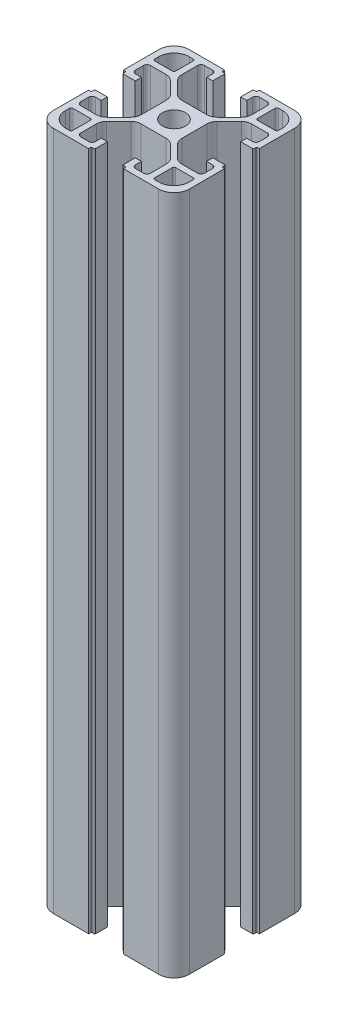
SolidWorks part; units mm, degrees
ref_plane "Front Plane" through (0, 0, 0) normal (0, 0, 1) x (1, 0, 0)
ref_plane "Top Plane" through (0, 0, 0) normal (0, 1, 0) x (1, 0, 0)
ref_plane "Right Plane" through (0, 0, 0) normal (1, 0, 0) x (0, 0, -1)
sketch "Sketch1" plane through (0, 0, 0) normal (0, 1, 0) x (1, 0, 0)
  line L0 (84.1702, 31.7204) -> (84.1702, 42.1204)
  line L1 (44.1702, 62.7204) -> (44.1702, 52.3204)
  line L2 (48.6702, 27.2204) -> (59.0702, 27.2204)
  line L3 (79.6702, 67.2204) -> (69.4702, 67.2204)
  line L4 (84.1702, 52.3204) -> (84.1702, 62.7204)
  line L5 (58.8702, 67.2204) -> (48.6702, 67.2204)
  line L6 (44.1702, 42.1204) -> (44.1702, 31.7204)
  line L7 (69.2702, 27.2204) -> (79.6702, 27.2204)
  line L10 (44.1702, 42.1204) -> (44.7702, 42.1204)
  line L11 (44.9702, 42.3204) -> (44.9702, 42.9204)
  line L12 (48.6702, 43.1204) -> (45.1702, 43.1204)
  line L13 (48.6702, 41.3204) -> (48.6702, 43.1204)
  line L14 (46.9702, 41.3204) -> (48.6702, 41.3204)
  line L15 (45.9702, 37.9704) -> (45.9702, 40.3204)
  line L16 (51.6169, 36.9704) -> (46.9702, 36.9704)
  line L17 (57.2915, 41.4024) -> (53.7382, 37.8491)
  line L18 (58.1702, 50.9171) -> (58.1702, 43.5237)
  line L19 (53.7382, 56.5917) -> (57.2915, 53.0384)
  line L20 (46.9702, 57.4704) -> (51.6169, 57.4704)
  line L21 (45.9702, 54.1204) -> (45.9702, 56.4704)
  line L22 (48.6702, 53.1204) -> (46.9702, 53.1204)
  line L23 (48.6702, 51.3204) -> (48.6702, 53.1204)
  line L24 (45.1702, 51.3204) -> (48.6702, 51.3204)
  line L25 (44.9702, 51.5204) -> (44.9702, 52.1204)
  line L26 (44.7702, 52.3204) -> (44.1702, 52.3204)
  line L29 (59.0702, 67.0204) -> (59.0702, 66.6204)
  line L30 (59.2702, 66.4204) -> (59.8702, 66.4204)
  line L31 (60.0702, 62.7204) -> (60.0702, 66.2204)
  line L32 (58.2702, 62.7204) -> (60.0702, 62.7204)
  line L33 (58.2702, 64.4204) -> (58.2702, 62.7204)
  line L34 (54.9202, 65.4204) -> (57.2702, 65.4204)
  line L35 (53.9202, 59.7737) -> (53.9202, 64.4204)
  line L36 (58.3522, 54.0991) -> (54.7989, 57.6524)
  line L37 (67.8669, 53.2204) -> (60.4735, 53.2204)
  line L38 (73.5415, 57.6524) -> (69.9882, 54.0991)
  line L39 (74.4202, 64.4204) -> (74.4202, 59.7737)
  line L40 (71.0702, 65.4204) -> (73.4202, 65.4204)
  line L41 (70.0702, 62.7204) -> (70.0702, 64.4204)
  line L42 (68.2702, 62.7204) -> (70.0702, 62.7204)
  line L43 (68.2702, 66.2204) -> (68.2702, 62.7204)
  line L44 (68.4702, 66.4204) -> (69.0702, 66.4204)
  line L45 (69.2702, 66.6204) -> (69.2702, 67.0204)
  line L48 (84.1702, 52.3204) -> (83.5702, 52.3204)
  line L49 (83.3702, 52.1204) -> (83.3702, 51.5204)
  line L50 (79.6702, 51.3204) -> (83.1702, 51.3204)
  line L51 (79.6702, 53.1204) -> (79.6702, 51.3204)
  line L52 (81.3702, 53.1204) -> (79.6702, 53.1204)
  line L53 (82.3702, 56.4704) -> (82.3702, 54.1204)
  line L54 (76.7235, 57.4704) -> (81.3702, 57.4704)
  line L55 (71.0489, 53.0384) -> (74.6022, 56.5917)
  line L56 (70.1702, 43.5237) -> (70.1702, 50.9171)
  line L57 (74.6022, 37.8491) -> (71.0489, 41.4024)
  line L58 (81.3702, 36.9704) -> (76.7235, 36.9704)
  line L59 (82.3702, 40.3204) -> (82.3702, 37.9704)
  line L60 (79.6702, 41.3204) -> (81.3702, 41.3204)
  line L61 (79.6702, 43.1204) -> (79.6702, 41.3204)
  line L62 (83.1702, 43.1204) -> (79.6702, 43.1204)
  line L63 (83.3702, 42.9204) -> (83.3702, 42.3204)
  line L64 (83.5702, 42.1204) -> (84.1702, 42.1204)
  line L67 (69.2702, 27.2204) -> (69.2702, 27.8204)
  line L68 (69.0702, 28.0204) -> (68.4702, 28.0204)
  line L69 (68.2702, 31.7204) -> (68.2702, 28.2204)
  line L70 (70.0702, 31.7204) -> (68.2702, 31.7204)
  line L71 (70.0702, 30.0204) -> (70.0702, 31.7204)
  line L72 (73.4202, 29.0204) -> (71.0702, 29.0204)
  line L73 (74.4202, 34.6671) -> (74.4202, 30.0204)
  line L74 (69.9882, 40.3417) -> (73.5415, 36.7884)
  line L75 (60.4735, 41.2204) -> (67.8669, 41.2204)
  line L76 (54.7989, 36.7884) -> (58.3522, 40.3417)
  line L77 (53.9202, 30.0204) -> (53.9202, 34.6671)
  line L78 (57.2702, 29.0204) -> (54.9202, 29.0204)
  line L79 (58.2702, 31.7204) -> (58.2702, 30.0204)
  line L80 (60.0702, 31.7204) -> (58.2702, 31.7204)
  line L81 (60.0702, 28.2204) -> (60.0702, 31.7204)
  line L82 (59.8702, 28.0204) -> (59.2702, 28.0204)
  line L83 (59.0702, 27.8204) -> (59.0702, 27.2204)
  line L84 (82.3702, 34.6704) -> (82.3702, 33.5204)
  line L85 (76.7202, 35.1704) -> (81.8702, 35.1704)
  line L86 (76.2202, 29.5204) -> (76.2202, 34.6704)
  line L87 (77.8702, 29.0204) -> (76.7202, 29.0204)
  line L88 (51.6202, 29.0204) -> (50.4702, 29.0204)
  line L89 (52.1202, 34.6704) -> (52.1202, 29.5204)
  line L90 (46.4702, 35.1704) -> (51.6202, 35.1704)
  line L91 (45.9702, 33.5204) -> (45.9702, 34.6704)
  line L92 (45.9702, 59.7704) -> (45.9702, 60.9204)
  line L93 (51.6202, 59.2704) -> (46.4702, 59.2704)
  line L94 (52.1202, 64.9204) -> (52.1202, 59.7704)
  line L95 (50.4702, 65.4204) -> (51.6202, 65.4204)
  line L96 (76.7202, 65.4204) -> (77.8702, 65.4204)
  line L97 (76.2202, 59.7704) -> (76.2202, 64.9204)
  line L98 (81.8702, 59.2704) -> (76.7202, 59.2704)
  line L99 (82.3702, 60.9204) -> (82.3702, 59.7704)
  arc A0 (60.7702, 47.2204) -> (67.5702, 47.2204) centre (64.1702, 47.2204) ccw
  arc A1 (44.1702, 31.7204) -> (48.6702, 27.2204) centre (48.6702, 31.7204) ccw
  arc A2 (44.7702, 42.1204) -> (44.9702, 42.3204) centre (44.7702, 42.3204) ccw
  arc A3 (45.1702, 43.1204) -> (44.9702, 42.9204) centre (45.1702, 42.9204) ccw
  arc A4 (46.9702, 41.3204) -> (45.9702, 40.3204) centre (46.9702, 40.3204) ccw
  arc A5 (45.9702, 37.9704) -> (46.9702, 36.9704) centre (46.9702, 37.9704) ccw
  arc A6 (51.6169, 36.9704) -> (53.7382, 37.8491) centre (51.6169, 39.9704) ccw
  arc A7 (57.2915, 41.4024) -> (58.1702, 43.5237) centre (55.1702, 43.5237) ccw
  arc A8 (58.1702, 50.9171) -> (57.2915, 53.0384) centre (55.1702, 50.9171) ccw
  arc A9 (53.7382, 56.5917) -> (51.6169, 57.4704) centre (51.6169, 54.4704) ccw
  arc A10 (46.9702, 57.4704) -> (45.9702, 56.4704) centre (46.9702, 56.4704) ccw
  arc A11 (45.9702, 54.1204) -> (46.9702, 53.1204) centre (46.9702, 54.1204) ccw
  arc A12 (44.9702, 51.5204) -> (45.1702, 51.3204) centre (45.1702, 51.5204) ccw
  arc A13 (44.9702, 52.1204) -> (44.7702, 52.3204) centre (44.7702, 52.1204) ccw
  arc A14 (48.6702, 67.2204) -> (44.1702, 62.7204) centre (48.6702, 62.7204) ccw
  arc A15 (59.0702, 67.0204) -> (58.8702, 67.2204) centre (58.8702, 67.0204) ccw
  arc A16 (59.0702, 66.6204) -> (59.2702, 66.4204) centre (59.2702, 66.6204) ccw
  arc A17 (60.0702, 66.2204) -> (59.8702, 66.4204) centre (59.8702, 66.2204) ccw
  arc A18 (58.2702, 64.4204) -> (57.2702, 65.4204) centre (57.2702, 64.4204) ccw
  arc A19 (54.9202, 65.4204) -> (53.9202, 64.4204) centre (54.9202, 64.4204) ccw
  arc A20 (53.9202, 59.7737) -> (54.7989, 57.6524) centre (56.9202, 59.7737) ccw
  arc A21 (58.3522, 54.0991) -> (60.4735, 53.2204) centre (60.4735, 56.2204) ccw
  arc A22 (67.8669, 53.2204) -> (69.9882, 54.0991) centre (67.8669, 56.2204) ccw
  arc A23 (73.5415, 57.6524) -> (74.4202, 59.7737) centre (71.4202, 59.7737) ccw
  arc A24 (74.4202, 64.4204) -> (73.4202, 65.4204) centre (73.4202, 64.4204) ccw
  arc A25 (71.0702, 65.4204) -> (70.0702, 64.4204) centre (71.0702, 64.4204) ccw
  arc A26 (68.4702, 66.4204) -> (68.2702, 66.2204) centre (68.4702, 66.2204) ccw
  arc A27 (69.0702, 66.4204) -> (69.2702, 66.6204) centre (69.0702, 66.6204) ccw
  arc A28 (69.4702, 67.2204) -> (69.2702, 67.0204) centre (69.4702, 67.0204) ccw
  arc A29 (84.1702, 62.7204) -> (79.6702, 67.2204) centre (79.6702, 62.7204) ccw
  arc A30 (83.5702, 52.3204) -> (83.3702, 52.1204) centre (83.5702, 52.1204) ccw
  arc A31 (83.1702, 51.3204) -> (83.3702, 51.5204) centre (83.1702, 51.5204) ccw
  arc A32 (81.3702, 53.1204) -> (82.3702, 54.1204) centre (81.3702, 54.1204) ccw
  arc A33 (82.3702, 56.4704) -> (81.3702, 57.4704) centre (81.3702, 56.4704) ccw
  arc A34 (76.7235, 57.4704) -> (74.6022, 56.5917) centre (76.7235, 54.4704) ccw
  arc A35 (71.0489, 53.0384) -> (70.1702, 50.9171) centre (73.1702, 50.9171) ccw
  arc A36 (70.1702, 43.5237) -> (71.0489, 41.4024) centre (73.1702, 43.5237) ccw
  arc A37 (74.6022, 37.8491) -> (76.7235, 36.9704) centre (76.7235, 39.9704) ccw
  arc A38 (81.3702, 36.9704) -> (82.3702, 37.9704) centre (81.3702, 37.9704) ccw
  arc A39 (82.3702, 40.3204) -> (81.3702, 41.3204) centre (81.3702, 40.3204) ccw
  arc A40 (83.3702, 42.9204) -> (83.1702, 43.1204) centre (83.1702, 42.9204) ccw
  arc A41 (83.3702, 42.3204) -> (83.5702, 42.1204) centre (83.5702, 42.3204) ccw
  arc A42 (79.6702, 27.2204) -> (84.1702, 31.7204) centre (79.6702, 31.7204) ccw
  arc A43 (69.2702, 27.8204) -> (69.0702, 28.0204) centre (69.0702, 27.8204) ccw
  arc A44 (68.2702, 28.2204) -> (68.4702, 28.0204) centre (68.4702, 28.2204) ccw
  arc A45 (70.0702, 30.0204) -> (71.0702, 29.0204) centre (71.0702, 30.0204) ccw
  arc A46 (73.4202, 29.0204) -> (74.4202, 30.0204) centre (73.4202, 30.0204) ccw
  arc A47 (74.4202, 34.6671) -> (73.5415, 36.7884) centre (71.4202, 34.6671) ccw
  arc A48 (69.9882, 40.3417) -> (67.8669, 41.2204) centre (67.8669, 38.2204) ccw
  arc A49 (60.4735, 41.2204) -> (58.3522, 40.3417) centre (60.4735, 38.2204) ccw
  arc A50 (54.7989, 36.7884) -> (53.9202, 34.6671) centre (56.9202, 34.6671) ccw
  arc A51 (53.9202, 30.0204) -> (54.9202, 29.0204) centre (54.9202, 30.0204) ccw
  arc A52 (57.2702, 29.0204) -> (58.2702, 30.0204) centre (57.2702, 30.0204) ccw
  arc A53 (59.8702, 28.0204) -> (60.0702, 28.2204) centre (59.8702, 28.2204) ccw
  arc A54 (59.2702, 28.0204) -> (59.0702, 27.8204) centre (59.2702, 27.8204) ccw
  arc A55 (82.3702, 34.6704) -> (81.8702, 35.1704) centre (81.8702, 34.6704) ccw
  arc A56 (76.7202, 35.1704) -> (76.2202, 34.6704) centre (76.7202, 34.6704) ccw
  arc A57 (76.2202, 29.5204) -> (76.7202, 29.0204) centre (76.7202, 29.5204) ccw
  arc A58 (77.8702, 29.0204) -> (82.3702, 33.5204) centre (77.8702, 33.5204) ccw
  arc A59 (51.6202, 29.0204) -> (52.1202, 29.5204) centre (51.6202, 29.5204) ccw
  arc A60 (52.1202, 34.6704) -> (51.6202, 35.1704) centre (51.6202, 34.6704) ccw
  arc A61 (46.4702, 35.1704) -> (45.9702, 34.6704) centre (46.4702, 34.6704) ccw
  arc A62 (45.9702, 33.5204) -> (50.4702, 29.0204) centre (50.4702, 33.5204) ccw
  arc A63 (45.9702, 59.7704) -> (46.4702, 59.2704) centre (46.4702, 59.7704) ccw
  arc A64 (51.6202, 59.2704) -> (52.1202, 59.7704) centre (51.6202, 59.7704) ccw
  arc A65 (52.1202, 64.9204) -> (51.6202, 65.4204) centre (51.6202, 64.9204) ccw
  arc A66 (50.4702, 65.4204) -> (45.9702, 60.9204) centre (50.4702, 60.9204) ccw
  arc A67 (76.7202, 65.4204) -> (76.2202, 64.9204) centre (76.7202, 64.9204) ccw
  arc A68 (76.2202, 59.7704) -> (76.7202, 59.2704) centre (76.7202, 59.7704) ccw
  arc A69 (81.8702, 59.2704) -> (82.3702, 59.7704) centre (81.8702, 59.7704) ccw
  arc A70 (82.3702, 60.9204) -> (77.8702, 65.4204) centre (77.8702, 60.9204) ccw
  arc A71 (67.5702, 47.2204) -> (60.7702, 47.2204) centre (64.1702, 47.2204) ccw
extrude "Boss-Extrude1" add sketch "Sketch1" along normal blind 200
